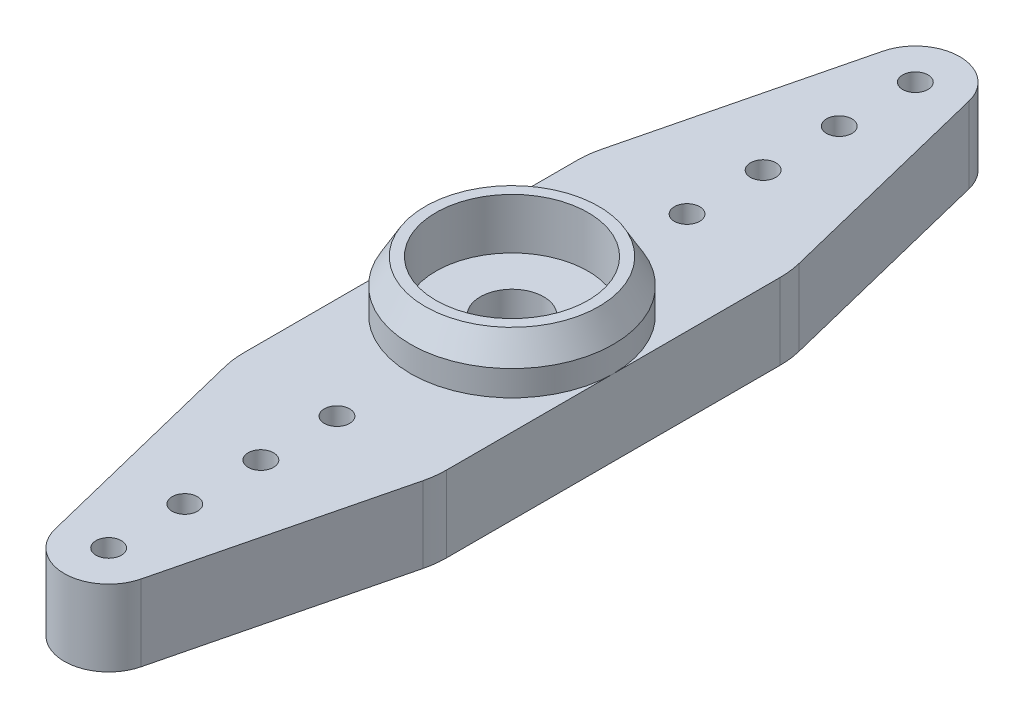
SolidWorks part; units mm, degrees
ref_plane "Alzado" through (0, 0, 0) normal (0, 0, 1) x (1, 0, 0)
ref_plane "Planta" through (0, 0, 0) normal (0, 1, 0) x (1, 0, 0)
ref_plane "Vista lateral" through (0, 0, 0) normal (1, 0, 0) x (0, 0, -1)
sketch "Croquis1" plane through (0, 0, 0) normal (0, 1, 0) x (1, 0, 0)
  line L0 (-4, 0) -> (-4, 6.5743)
  line L1 (-3.898, 7.4133) -> (-1.699, 16.3191)
  line L2 (1.699, 16.3191) -> (3.898, 7.4133)
  line L3 (4, 6.5743) -> (4, 0)
  line L4 (4, 0) -> (1.25, 0)
  line L5 (-4, 0) -> (-1.25, 0)
  line L6 (0, 0) -> (0, 23.2) construction
  arc A0 (1.25, 0) -> (-1.25, 0) centre (0, 0) ccw
  arc A1 (-1.699, 16.3191) -> (1.699, 16.3191) centre (0, 15.8996) cw
  arc A2 (-4, 6.5743) -> (-3.898, 7.4133) centre (-0.5, 6.5743) cw
  arc A3 (3.898, 7.4133) -> (4, 6.5743) centre (0.5, 6.5743) cw
  circle A4 centre (0, 15.8996) radius 0.5
  circle A5 centre (0, 12.8996) radius 0.5
  circle A6 centre (0, 9.8996) radius 0.5
  circle A7 centre (0, 6.8996) radius 0.5
  point P14 (-4, 7)
  dimension "D1" = 1.25
  dimension "D5" = 1.75
  dimension "D6" = 3.5
  dimension "D7" = 1
  dimension "D2" = 8
  dimension "D3" = 7
  dimension "D4" = 23.2
  dimension "D8" = 4
extrude "Saliente-Extruir1" add sketch "Croquis1" along normal blind 3
pattern_circular "MatrizC1" count 2 every 180 about axis through (0, 0, 0) along (0, 1, 0) of "Saliente-Extruir1"
sketch "Croquis2" plane through (0, 3, 0) normal (0, 1, 0) x (1, 0, 0)
  circle A0 centre (0, 0) radius 3
  circle A1 centre (0, 0) radius 4
  dimension "D1" = 6
  dimension "D2" = 8
extrude "Saliente-Extruir2" add sketch "Croquis2" along normal blind 2
chamfer "Chaflán1" distance 1 angle 30 1 edges at (0, 5, 4)
